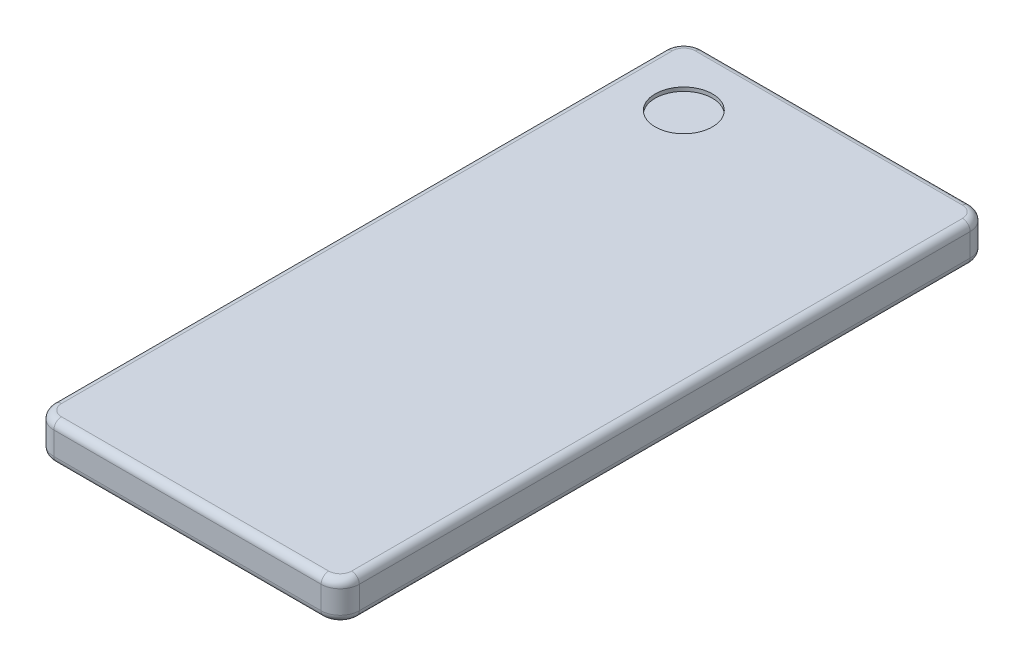
SolidWorks part; units mm, degrees
ref_plane "Front Plane" through (0, 0, 0) normal (0, 0, 1) x (1, 0, 0)
ref_plane "Top Plane" through (0, 0, 0) normal (0, 1, 0) x (1, 0, 0)
ref_plane "Right Plane" through (0, 0, 0) normal (1, 0, 0) x (0, 0, -1)
sketch "Sketch1" plane through (0, 0, 0) normal (0, 1, 0) x (1, 0, 0)
  line L1 (-40, 85) -> (40, 85)
  line L2 (-40, 85) -> (-40, -85)
  line L3 (-40, -85) -> (40, -85)
  line L4 (40, 85) -> (40, -85)
  line L5 (-40, 85) -> (40, -85) construction
  line L6 (-40, -85) -> (40, 85) construction
  point P0 (0, 0)
  dimension "D1" = 170
  dimension "D2" = 80
extrude "Boss-Extrude1" add sketch "Sketch1" along normal blind 10
fillet "Fillet4" radius 5 4 edges at (40, 5, -85) (-40, 5, -85) (-40, 5, 85) (40, 5, 85)
fillet "Fillet5" radius 2 16 edges at (-38.5355, 0, 83.5355) (-40, 0, 0) (-38.5355, 0, -83.5355) (0, 0, -85) (38.5355, 0, -83.5355) (40, 0, 0) (38.5355, 0, 83.5355) (-38.5355, 10, -83.5355) (0, 10, -85) (38.5355, 10, -83.5355) (40, 10, 0) (38.5355, 10, 83.5355) (0, 10, 85) (-38.5355, 10, 83.5355) (0, 0, 85) (-40, 10, 0)
sketch "Sketch3" plane through (0, 10, 0) normal (0, 1, 0) x (1, 0, 0)
  line L0 (0, 83) -> (0, -83) construction
  line L1 (35, 83) -> (-35, 83) construction
  line L2 (-35, -83) -> (35, -83) construction
  line L3 (38, 0) -> (-38, 0) construction
  line L4 (38, -80) -> (38, 80) construction
  line L5 (-38, 80) -> (-38, -80) construction
  circle A0 centre (-23, 68) radius 7.5
  dimension "D1" = 15
  dimension "D2" = 15
  dimension "D3" = 15
extrude "Cut-Extrude1" cut sketch "Sketch3" against normal blind 1
